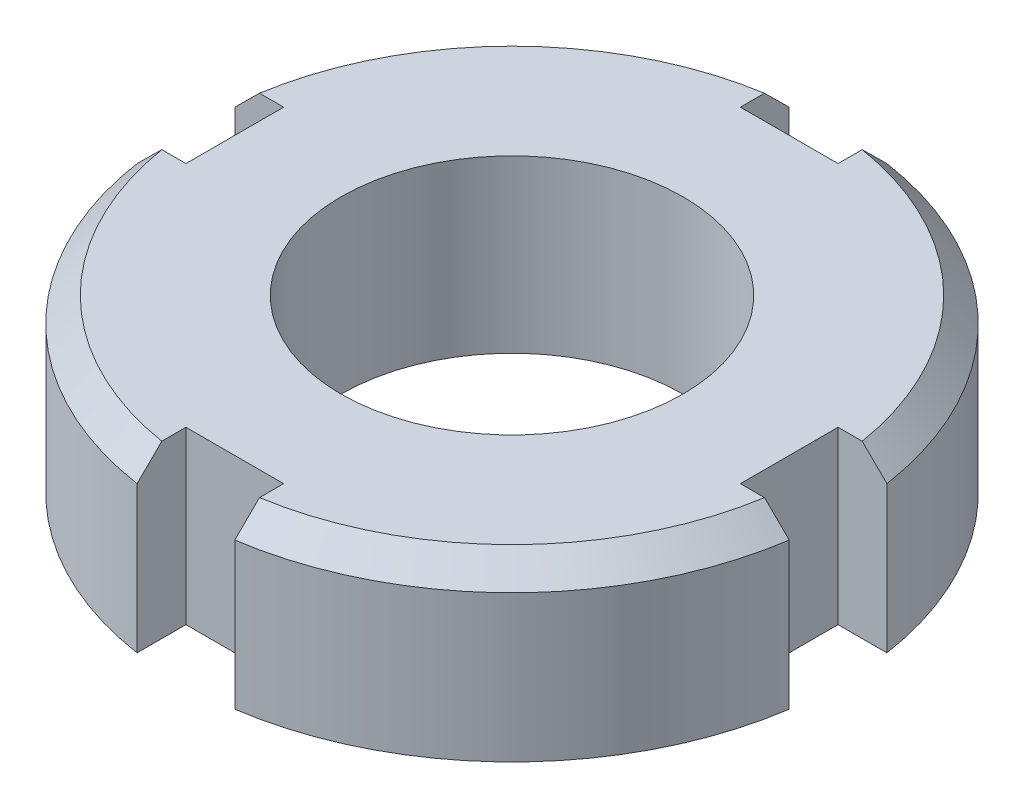
SolidWorks part; units mm, degrees
material "Plain Carbon Steel"
ref_plane "Front Plane" through (0, 0, 0) normal (0, 0, 1) x (1, 0, 0)
ref_plane "Top Plane" through (0, 0, 0) normal (0, 1, 0) x (1, 0, 0)
ref_plane "Right Plane" through (0, 0, 0) normal (1, 0, 0) x (0, 0, -1)
sketch "Sketch1" plane through (0, 0, 0) normal (0, 1, 0) x (1, 0, 0)
  circle A0 centre (0, 0) radius 13.5
  dimension "D1" = 27
extrude "Boss-Extrude1" add sketch "Sketch1" along normal mid plane 7
sketch "Sketch2" plane through (0, 0, 0) normal (0, 1, 0) x (1, 0, 0)
  line L0 (-2, 13.351) -> (-2, 11.351)
  line L1 (-2, 11.351) -> (2, 11.351)
  line L2 (2, 11.351) -> (2, 13.351)
  line L3 (13.351, 2) -> (11.351, 2)
  line L4 (11.351, 2) -> (11.351, -2)
  line L5 (11.351, -2) -> (13.351, -2)
  line L6 (2, -13.351) -> (2, -11.351)
  line L7 (2, -11.351) -> (-2, -11.351)
  line L8 (-2, -11.351) -> (-2, -13.351)
  line L9 (-13.351, -2) -> (-11.351, -2)
  line L10 (-11.351, -2) -> (-11.351, 2)
  line L11 (-11.351, 2) -> (-13.351, 2)
  circle A0 centre (0, 0) radius 13.5 construction
  arc A1 (2, 13.351) -> (-2, 13.351) centre (0, 0) ccw
  arc A2 (13.351, -2) -> (13.351, 2) centre (0, 0) ccw
  arc A3 (-2, -13.351) -> (2, -13.351) centre (0, 0) ccw
  arc A4 (-13.351, 2) -> (-13.351, -2) centre (0, 0) ccw
  point P23 (0, 0)
  dimension "D1" = 2
  dimension "D2" = 2
  dimension "D3" = 4
extrude "Cut-Extrude1" cut sketch "Sketch2" against normal through all both and the other way through all
chamfer "Chamfer1" distance 1 angle 45 4 edges at (-9.5459, 3.5, -9.5459) (9.5459, 3.5, -9.5459) (9.5459, 3.5, 9.5459) (-9.5459, 3.5, 9.5459)
sketch "Sketch3" plane through (0, 3.5, 0) normal (0, 1, 0) x (1, 0, 0)
  point P0 (0, 0)
hole_wizard "M16 Tapped Hole1" positions "Sketch3" profile "Sketch4" tap size "M16" standard "ISO" end condition up to next
sketch "Sketch4" plane through (0, 3.5, 0) normal (1, 0, 0) x (0, 0, 1)
  line L0 (0, 0) -> (0, 7)
  line L1 (0, 7) -> (7, 7)
  line L2 (7, 7) -> (7, 0)
  line L5 (7, 0) -> (0, 0)
  line L11 (0, -6.35) -> (0, 107.95) construction
  dimension "Thru Tap Drill Dia." = 14
  dimension "Thru Tap Drill Depth" = 7
cosmetic thread "Hole Thread1" parameters "D2"=16
